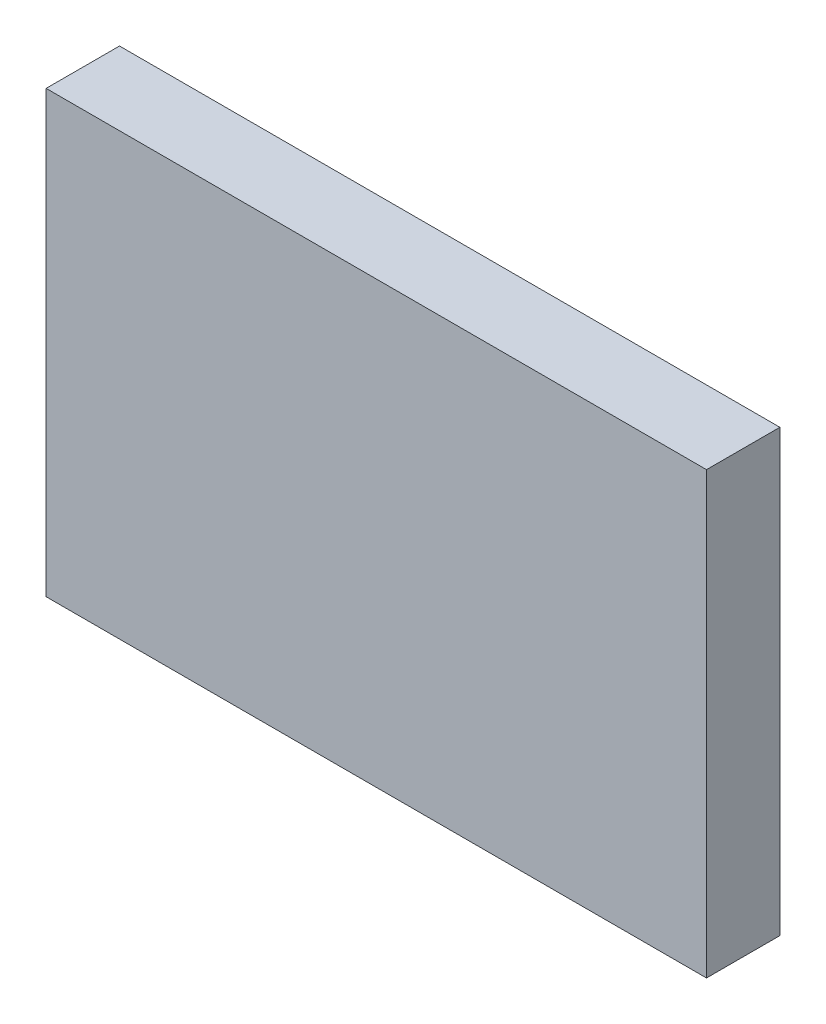
SolidWorks part; units mm, degrees
ref_plane "Front Plane" through (0, 0, 0) normal (0, 0, 1) x (1, 0, 0)
ref_plane "Top Plane" through (0, 0, 0) normal (0, 1, 0) x (1, 0, 0)
ref_plane "Right Plane" through (0, 0, 0) normal (1, 0, 0) x (0, 0, -1)
sketch "Sketch1" plane through (0, 0, 0) normal (0, 0, 1) x (1, 0, 0)
  line L1 (0, 0) -> (180, 0)
  line L2 (0, 0) -> (0, 120)
  line L3 (0, 120) -> (180, 120)
  line L4 (180, 0) -> (180, 120)
  dimension "D1" = 180
  dimension "D2" = 120
extrude "Boss-Extrude1" add sketch "Sketch1" along normal blind 20
